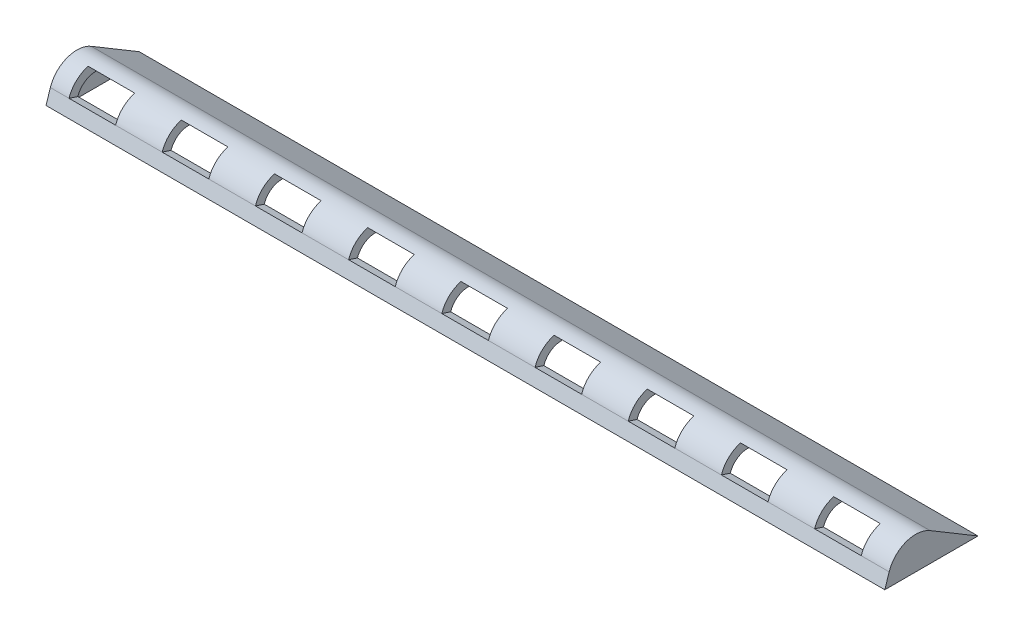
SolidWorks part; units mm, degrees
ref_plane "Front Plane" through (0, 0, 0) normal (0, 0, 1) x (1, 0, 0)
ref_plane "Top Plane" through (0, 0, 0) normal (0, 1, 0) x (1, 0, 0)
ref_plane "Right Plane" through (0, 0, 0) normal (1, 0, 0) x (0, 0, -1)
sketch "Sketch1" plane through (0, 0, 0) normal (1, 0, 0) x (0, 0, -1)
  line L0 (0, 0) -> (0.4684, 1.4314)
  line L1 (4.859, 3.0734) -> (10, 0)
  line L2 (10, 0) -> (0, 0)
  arc A0 (4.859, 3.0734) -> (0.4684, 1.4314) centre (3.3196, 0.4984) ccw
  point P6 (1.6361, 5)
  dimension "D3" = 3
  dimension "D1" = 10
  dimension "D2" = 5
extrude "Boss-Extrude1" add sketch "Sketch1" along normal blind 90
shell "Shell1" thickness 1
sketch "Sketch2" plane through (0, 0, 0) normal (0, 0.311, 0.9504) x (1, 0, 0)
  line L0 (90, 1.5061) -> (0, 1.5061) construction
  line L1 (2, 1.5061) -> (7, 1.5061)
  line L2 (2, 1.5061) -> (2, 4.0061)
  line L3 (2, 4.0061) -> (7, 4.0061)
  line L4 (7, 1.5061) -> (7, 4.0061)
  line L5 (12, 1.5061) -> (12, 4.0061)
  line L6 (12, 1.5061) -> (17, 1.5061)
  line L7 (17, 1.5061) -> (17, 4.0061)
  line L8 (12, 4.0061) -> (17, 4.0061)
  line L9 (22, 1.5061) -> (22, 4.0061)
  line L10 (22, 1.5061) -> (27, 1.5061)
  line L11 (27, 1.5061) -> (27, 4.0061)
  line L12 (22, 4.0061) -> (27, 4.0061)
  line L13 (32, 1.5061) -> (32, 4.0061)
  line L14 (32, 1.5061) -> (37, 1.5061)
  line L15 (37, 1.5061) -> (37, 4.0061)
  line L16 (32, 4.0061) -> (37, 4.0061)
  line L17 (42, 1.5061) -> (42, 4.0061)
  line L18 (42, 1.5061) -> (47, 1.5061)
  line L19 (47, 1.5061) -> (47, 4.0061)
  line L20 (42, 4.0061) -> (47, 4.0061)
  line L21 (52, 1.5061) -> (52, 4.0061)
  line L22 (52, 1.5061) -> (57, 1.5061)
  line L23 (57, 1.5061) -> (57, 4.0061)
  line L24 (52, 4.0061) -> (57, 4.0061)
  line L25 (62, 1.5061) -> (62, 4.0061)
  line L26 (62, 1.5061) -> (67, 1.5061)
  line L27 (67, 1.5061) -> (67, 4.0061)
  line L28 (62, 4.0061) -> (67, 4.0061)
  line L29 (72, 1.5061) -> (72, 4.0061)
  line L30 (72, 1.5061) -> (77, 1.5061)
  line L31 (77, 1.5061) -> (77, 4.0061)
  line L32 (72, 4.0061) -> (77, 4.0061)
  line L33 (82, 1.5061) -> (82, 4.0061)
  line L34 (82, 1.5061) -> (87, 1.5061)
  line L35 (87, 1.5061) -> (87, 4.0061)
  line L36 (82, 4.0061) -> (87, 4.0061)
  dimension "D1" = 2
  dimension "D2" = 5
  dimension "D3" = 2.5
  dimension "D4" = 9
extrude "Cut-Extrude2" cut sketch "Sketch2" against normal blind 3
